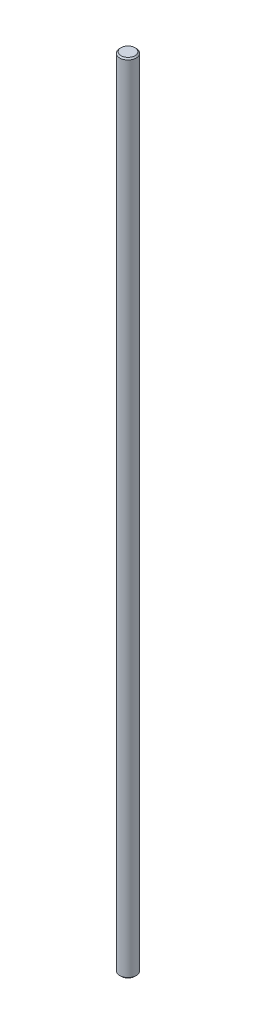
SolidWorks part; units mm, degrees
ref_plane "Front Plane" through (0, 0, 0) normal (0, 0, 1) x (1, 0, 0)
ref_plane "Top Plane" through (0, 0, 0) normal (0, 1, 0) x (1, 0, 0)
ref_plane "Right Plane" through (0, 0, 0) normal (1, 0, 0) x (0, 0, -1)
ref_plane "Plane1" through (0, 0, 0) normal (0, 0, -1) x (-1, 0, 0)
sketch "Sketch1" plane through (0, 0, 0) normal (0, 0, -1) x (-1, 0, 0)
  line L0 (-2.6632, 0) -> (0, 0)
  line L1 (0, 0) -> (0, 304.8)
  line L2 (0, 304.8) -> (-2.6632, 304.8)
  line L3 (-2.6632, 304.8) -> (-3.1712, 304.292)
  line L4 (-3.1712, 304.292) -> (-3.1712, 0.508)
  line L5 (-3.1712, 0.508) -> (-2.6632, 0)
  line L6 (0, 0) -> (0, 304.8) construction
revolve "Revolve1" add sketch "Sketch1" angle 360 about L6
